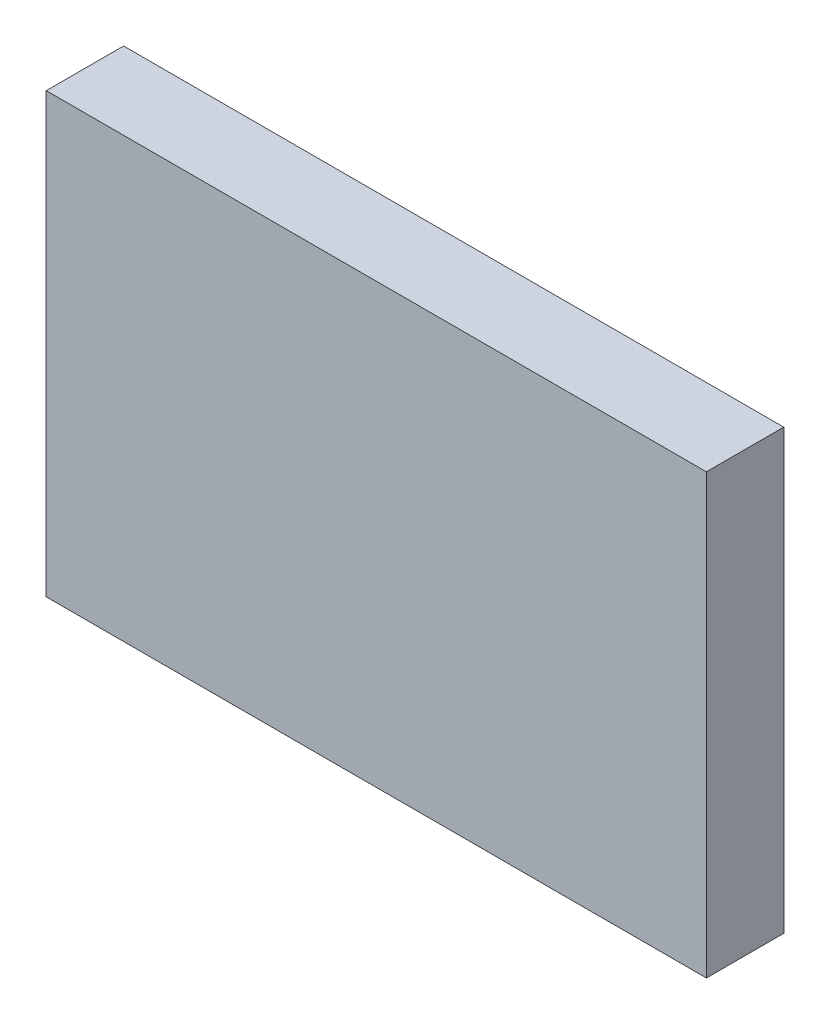
SolidWorks part; units mm, degrees
material "Oak"
ref_plane "Front Plane" through (0, 0, 0) normal (0, 0, 1) x (1, 0, 0)
ref_plane "Top Plane" through (0, 0, 0) normal (0, 1, 0) x (1, 0, 0)
ref_plane "Right Plane" through (0, 0, 0) normal (1, 0, 0) x (0, 0, -1)
sketch "Sketch1" plane through (0, 0, 0) normal (0, 0, 1) x (1, 0, 0)
  line L1 (0, 0) -> (-162.56, 0)
  line L2 (0, 0) -> (0, 107.95)
  line L3 (0, 107.95) -> (-162.56, 107.95)
  line L4 (-162.56, 0) -> (-162.56, 107.95)
  dimension "D1" = 162.56
  dimension "D2" = 107.95
extrude "Boss-Extrude1" add sketch "Sketch1" along normal blind 19.05
